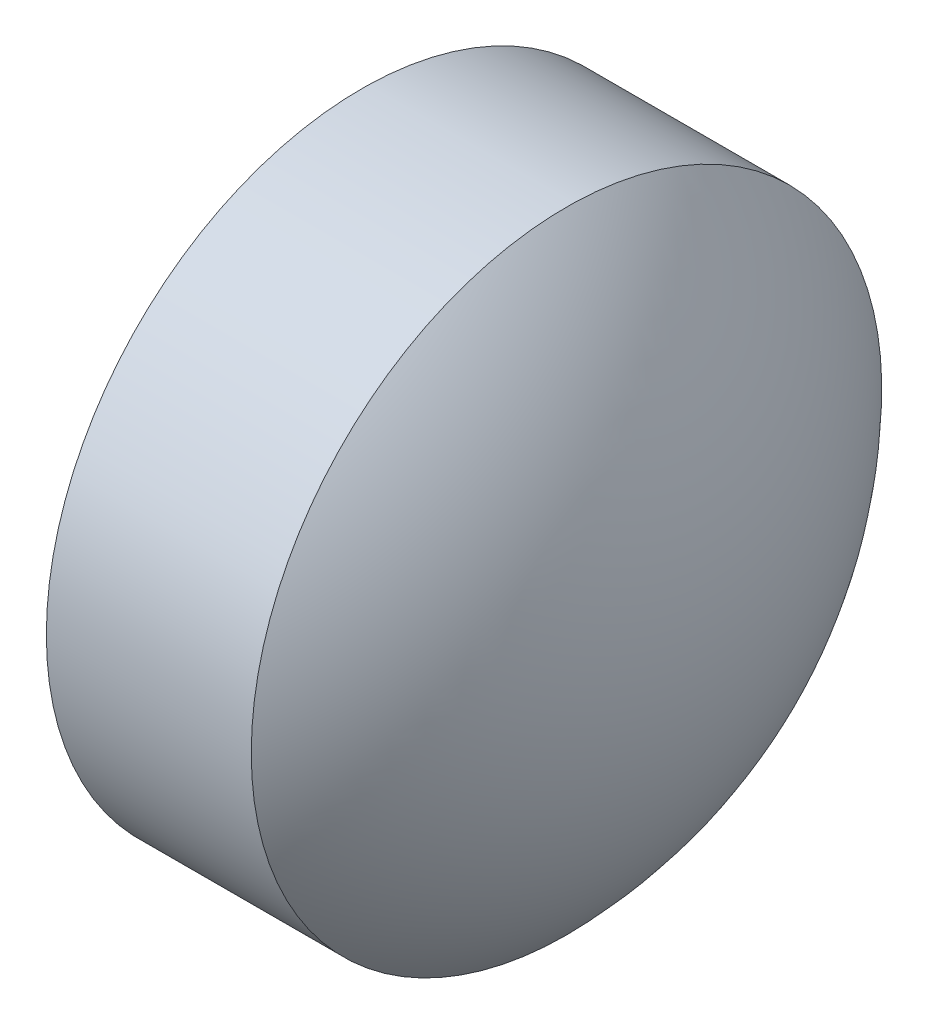
SolidWorks part; units mm, degrees
ref_plane "前视基准面" through (0, 0, 0) normal (0, 0, 1) x (1, 0, 0)
ref_plane "上视基准面" through (0, 0, 0) normal (0, 1, 0) x (1, 0, 0)
ref_plane "右视基准面" through (0, 0, 0) normal (1, 0, 0) x (0, 0, -1)
sketch "草图1" plane through (0, 0, 0) normal (0, 0, 1) x (1, 0, 0)
  line L0 (368.9339, 55.6768) -> (371.6314, 55.6768) construction
  line L1 (369.362, 55.6768) -> (369.362, 57.6768)
  line L2 (371.472, 55.6768) -> (369.362, 55.6768)
  line L5 (369.362, 57.6768) -> (370.662, 57.6768)
  arc A0 (371.472, 55.6768) -> (370.662, 57.6768) centre (368.5979, 55.6768) ccw
revolve "旋转1" add sketch "草图1" angle 360 about L0
